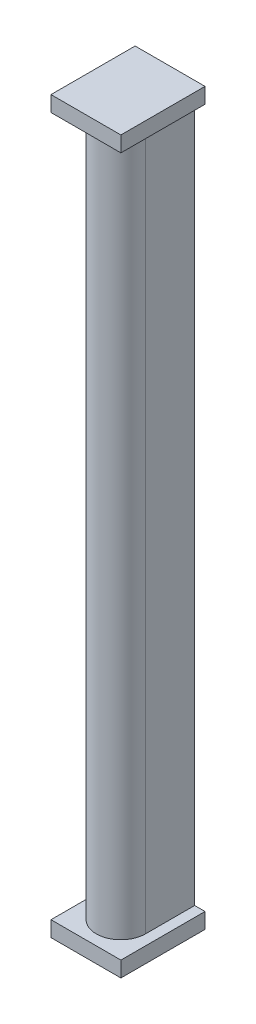
SolidWorks part; units mm, degrees
ref_plane "Front Plane" through (0, 0, 0) normal (0, 0, 1) x (1, 0, 0)
ref_plane "Top Plane" through (0, 0, 0) normal (0, 1, 0) x (1, 0, 0)
ref_plane "Right Plane" through (0, 0, 0) normal (1, 0, 0) x (0, 0, -1)
sketch "Sketch5" plane through (0, 0, 0) normal (0, 1, 0) x (1, 0, 0)
  line L1 (0, 0) -> (9.5, 0)
  line L2 (0, 0) -> (0, -9.5)
  line L4 (9.5, 0) -> (9.5, -9.5)
  arc A0 (0, -9.5) -> (9.5, -9.5) centre (4.75, -9.5) ccw
  dimension "D2" = 9.5
  dimension "D1" = 4.75
  dimension "D3" = 9.5
extrude "Boss-Extrude1" add sketch "Sketch5" against normal blind 135
sketch "Sketch8" plane through (0, -135, 0) normal (0, -1, 0) x (1, 0, 0)
  line L0 (0, 0) -> (0, 9.5) construction
  line L1 (-2, 0) -> (11.5, 0)
  line L2 (-2, 0) -> (-2, 16.25)
  line L3 (-2, 16.25) -> (11.5, 16.25)
  line L4 (11.5, 0) -> (11.5, 16.25)
  line L5 (9.5, 9.5) -> (9.5, 0) construction
  arc A0 (9.5, 9.5) -> (0, 9.5) centre (4.75, 9.5) ccw construction
  point P6 (4.75, 14.25)
  dimension "D1" = 2
  dimension "D2" = 2
  dimension "D3" = 2
extrude "Boss-Extrude4" add sketch "Sketch8" along normal blind 3
sketch "Sketch9" plane through (0, 0, 0) normal (0, 1, 0) x (1, 0, 0)
  line L1 (-2, 0) -> (11.5, 0)
  line L2 (-2, 0) -> (-2, -16.25)
  line L3 (-2, -16.25) -> (11.5, -16.25)
  line L4 (11.5, 0) -> (11.5, -16.25)
extrude "Boss-Extrude5" add sketch "Sketch9" along normal blind 3
